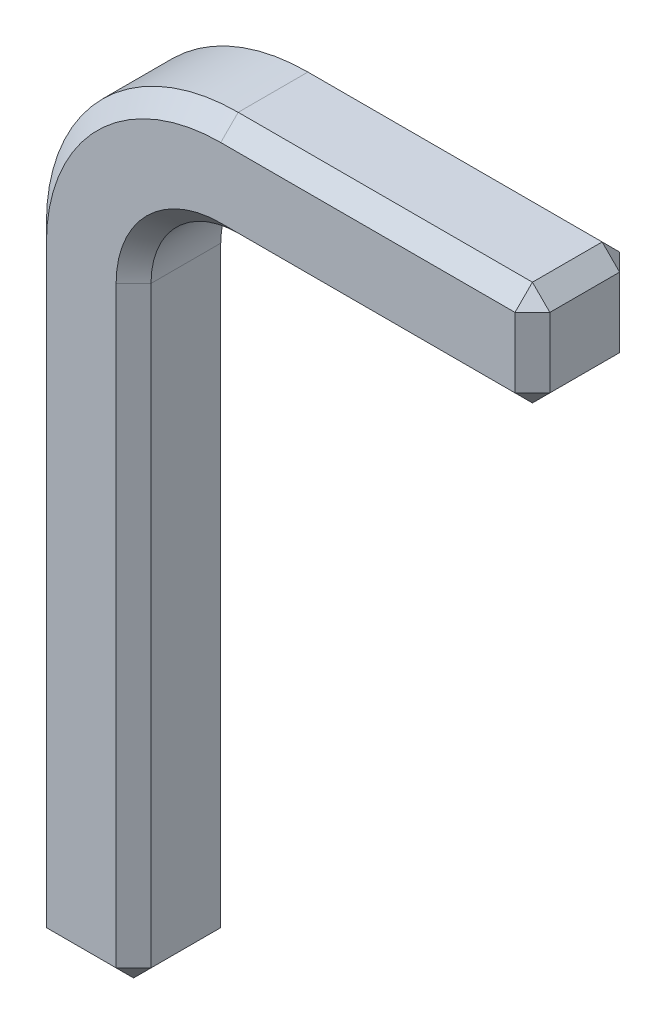
SolidWorks part; units mm, degrees
ref_plane "Front" through (0, 0, 0) normal (0, 0, 1) x (1, 0, 0)
ref_plane "Top" through (0, 0, 0) normal (0, 1, 0) x (1, 0, 0)
ref_plane "Right" through (0, 0, 0) normal (1, 0, 0) x (0, 0, -1)
sketch "Sketch1" plane through (0, 0, 0) normal (0, 0, 1) x (1, 0, 0)
  line L0 (-0.6, 0) -> (-0.6, 3.5)
  line L1 (0, 0) -> (0, 3.5)
  line L2 (0.5, 4) -> (2.2877, 4)
  line L3 (0.5, 4.6) -> (2.2877, 4.6)
  line L4 (2.2877, 4.6) -> (2.2877, 4)
  line L5 (-0.6, 0) -> (0, 0)
  arc A0 (0, 3.5) -> (0.5, 4) centre (0.5, 3.5) cw
  arc A1 (-0.6, 3.5) -> (0.5, 4.6) centre (0.5, 3.5) cw
  dimension "D1" = 4
  dimension "D3" = 0.5
  dimension "D2" = 0.6
extrude "Boss-Extrude1" add sketch "Sketch1" along normal mid plane 0.6
chamfer "Chamfer1" distance 0.1 angle 45 20 edges at (-0.6, 0, 0) (-0.3, 0, 0.3) (0, 0, 0) (-0.3, 0, -0.3) (2.2877, 4, 0) (2.2877, 4.3, 0.3) (2.2877, 4.6, 0) (2.2877, 4.3, -0.3) (0, 1.75, -0.3) (0.1464, 3.8536, -0.3) (1.3938, 4, -0.3) (1.3938, 4.6, -0.3) (-0.2778, 4.2778, -0.3) (-0.6, 1.75, -0.3) (-0.6, 1.75, 0.3) (-0.2778, 4.2778, 0.3) (1.3938, 4.6, 0.3) (0, 1.75, 0.3) (0.1464, 3.8536, 0.3) (1.3938, 4, 0.3)
sketch "Sketch2" plane through (0, 0, 0) normal (0, 0, 1) x (1, 0, 0)
  line L0 (-0.3, 0) -> (-0.3, 3.2516) construction
  line L1 (-0.1, 0) -> (-0.5, 0) construction
